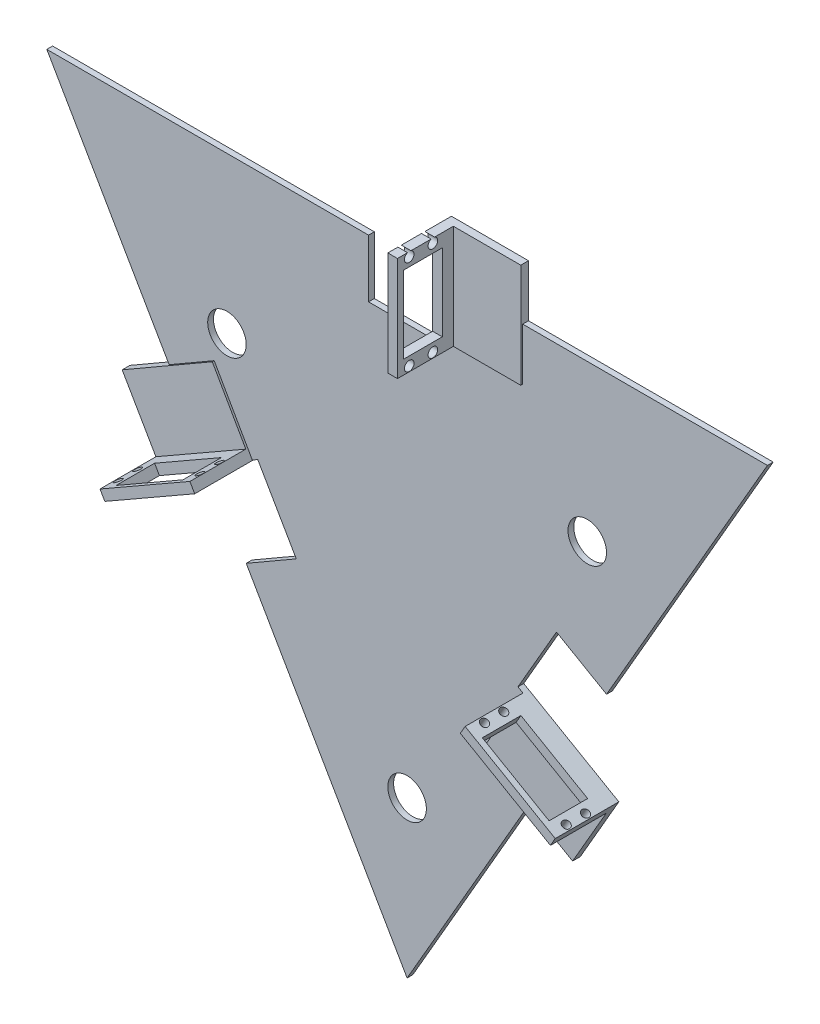
SolidWorks part; units mm, degrees
ref_plane "Front Plane" through (0, 0, 0) normal (0, 0, 1) x (1, 0, 0)
ref_plane "Top Plane" through (0, 0, 0) normal (0, 1, 0) x (1, 0, 0)
ref_plane "Right Plane" through (0, 0, 0) normal (1, 0, 0) x (0, 0, -1)
sketch "Sketch2" plane through (0, 0, 0) normal (0, 0, 1) x (1, 0, 0)
  line L0 (0, 161.9468) -> (0, -161.9468) construction
  line L1 (-187, 161.9468) -> (187, 161.9468)
  line L2 (187, 161.9468) -> (0, -161.9468)
  line L3 (-187, 161.9468) -> (0, -161.9468)
  point P4 (0, 0)
  point P8 (0, 161.9468)
  dimension "D1" = 374
  dimension "D2" = 374
  dimension "D3" = 374
extrude "Boss-Extrude1" add sketch "Sketch2" along normal blind 3
sketch "Sketch3" plane through (0, 0, 0) normal (0, 0, 1) x (1, 0, 0)
  line L1 (-187, 161.9468) -> (0, -161.9468) construction
  line L2 (-83.5, -17.3205) -> (-57.5192, -2.3205)
  line L6 (-103.5, 17.3205) -> (-77.5192, 32.3205)
  line L9 (0, -161.9468) -> (187, 161.9468) construction
  line L11 (57.5192, -2.3205) -> (83.5, -17.3205)
  line L13 (103.5, 17.3205) -> (77.5192, 32.3205)
  line L16 (187, 161.9468) -> (-187, 161.9468) construction
  line L18 (20, 131.9468) -> (20, 161.9468)
  line L20 (-20, 161.9468) -> (-20, 131.9468)
  line L22 (-103.5, 17.3205) -> (-83.5, -17.3205)
  line L23 (83.5, -17.3205) -> (103.5, 17.3205)
  line L24 (-20, 161.9468) -> (20, 161.9468)
  line L25 (-77.5192, 32.3205) -> (-57.5192, -2.3205)
  line L26 (-20, 161.9468) -> (20, 161.9468)
  line L27 (-20, 161.9468) -> (-20, 131.9468)
  line L28 (-20, 131.9468) -> (20, 131.9468)
  line L29 (20, 161.9468) -> (20, 131.9468)
  line L30 (77.5192, 32.3205) -> (57.5192, -2.3205)
  dimension "D1" = 30
  dimension "D4" = 30
  dimension "D6" = 30
extrude "Cut-Extrude2" cut sketch "Sketch3" along normal blind 10 contours L30 L11 L23 L13 | L25 L2 L22 L6
sketch "Sketch4" plane through (0, 0, 0) normal (0, 0, 1) x (1, 0, 0)
  line L1 (187, 161.9468) -> (-187, 161.9468) construction
  line L2 (0, 131.9468) -> (20, 131.9468)
  line L3 (20, 131.9468) -> (20, 161.9468)
  line L4 (20, 161.9468) -> (0, 161.9468)
  line L5 (0, 161.9468) -> (-20, 161.9468)
  line L6 (-20, 161.9468) -> (-20, 131.9468)
  line L7 (-20, 131.9468) -> (0, 131.9468)
  dimension "D1" = 20
  dimension "D2" = 20
  dimension "D3" = 30
extrude "Cut-Extrude3" cut sketch "Sketch4" along normal blind 10
sketch "Sketch5" plane through (0, 0, 0) normal (0, 0, 1) x (1, 0, 0)
  line L0 (-103.5, 17.3205) -> (-80.2543, 30.544)
  line L1 (-80.2543, 30.544) -> (-100.1173, 65.4615)
  line L2 (-100.1173, 65.4615) -> (-123.5, 51.9615)
  line L3 (-187, 161.9468) -> (-103.5, 17.3205) construction
  line L5 (-103.5, 17.3205) -> (-126.8827, 3.8205)
  line L6 (-126.8827, 3.8205) -> (-146.8827, 38.4615)
  line L7 (-146.8827, 38.4615) -> (-123.5, 51.9615)
  line L16 (20, 161.9468) -> (20, 134.9468)
  line L17 (20, 134.9468) -> (60, 134.9468)
  line L18 (60, 134.9468) -> (60, 161.9468)
  line L19 (187, 161.9468) -> (20, 161.9468) construction
  line L21 (20, 161.9468) -> (20, 188.9468)
  line L22 (20, 188.9468) -> (60, 188.9468)
  line L23 (60, 188.9468) -> (60, 161.9468)
  line L24 (83.5, -17.3205) -> (60.1173, -3.8205)
  line L25 (60.1173, -3.8205) -> (40.1173, -38.4615)
  line L26 (40.1173, -38.4615) -> (63.5, -51.9615)
  line L27 (0, -161.9468) -> (83.5, -17.3205) construction
  line L29 (83.5, -17.3205) -> (106.8827, -30.8205)
  line L30 (106.8827, -30.8205) -> (86.8827, -65.4615)
  line L31 (86.8827, -65.4615) -> (63.5, -51.9615)
  dimension "D1" = 40
  dimension "D2" = 27
  dimension "D3" = 27
  dimension "D7" = 27
  dimension "D8" = 27
  dimension "D9" = 40
  dimension "D10" = 40
  dimension "D11" = 27
  dimension "D12" = 27
extrude "Boss-Extrude2" add sketch "Sketch5" along normal blind 4
sketch "Sketch6" plane through (0, 0, 3) normal (0, 0, 1) x (1, 0, 0)
  line L0 (-126.8827, 3.8205) -> (-80.2543, 30.544)
  line L1 (-80.2543, 30.544) -> (-82.7265, 34.89)
  line L2 (-80.2543, 30.544) -> (-100.1173, 65.4615) construction
  line L3 (-82.7265, 34.89) -> (-129.3827, 8.1506)
  line L4 (-146.8827, 38.4615) -> (-126.8827, 3.8205) construction
  line L5 (-129.3827, 8.1506) -> (-126.8827, 3.8205)
  line L6 (60.1173, -3.8205) -> (106.8827, -30.8205)
  line L7 (106.8827, -30.8205) -> (104.3827, -35.1506)
  line L8 (86.8827, -65.4615) -> (106.8827, -30.8205) construction
  line L12 (20, 134.9468) -> (20, 188.9468)
  line L13 (20, 188.9468) -> (25, 188.9468)
  line L14 (60, 188.9468) -> (20, 188.9468) construction
  line L15 (25, 188.9468) -> (25, 134.9468)
  line L16 (20, 134.9468) -> (60, 134.9468) construction
  line L17 (25, 134.9468) -> (20, 134.9468)
  line L18 (104.3827, -35.1506) -> (57.6173, -8.1506)
  line L19 (60.1173, -3.8205) -> (40.1173, -38.4615) construction
  line L20 (57.6173, -8.1506) -> (60.1173, -3.8205)
  dimension "D1" = 5
  dimension "D2" = 5
  dimension "D3" = 5
  dimension "D4" = 5
extrude "Boss-Extrude3" add sketch "Sketch6" along normal blind 30
sketch "Sketch8" plane through (-33.0199, 57.6147, 0) normal (0.4972, -0.8676, 0) x (0.8676, 0.4972, 0)
  line L0 (-108.2287, 20.7043) -> (-54.2287, 20.7043) construction
  line L1 (-101.2287, 30.7043) -> (-61.2287, 30.7043)
  line L2 (-101.2287, 30.7043) -> (-101.2287, 10.7043)
  line L3 (-101.2287, 10.7043) -> (-61.2287, 10.7043)
  line L4 (-61.2287, 30.7043) -> (-61.2287, 10.7043)
  line L5 (-101.2287, 30.7043) -> (-61.2287, 10.7043) construction
  line L6 (-101.2287, 10.7043) -> (-61.2287, 30.7043) construction
  circle A0 centre (-56.7287, 15.7043) radius 2
  circle A1 centre (-56.7287, 25.7043) radius 2
  circle A2 centre (-105.7287, 25.7043) radius 2
  circle A3 centre (-105.7287, 15.7043) radius 2
  point P3 (-81.2287, 20.7043)
  point P8 (-81.2287, 20.7043)
  dimension "D1" = 5
  dimension "D2" = 5
  dimension "D3" = 4.5
  dimension "D4" = 4.5
  dimension "D5" = 4.5
  dimension "D6" = 5
  dimension "D7" = 5
  dimension "D8" = 4.5
extrude "Cut-Extrude4" cut sketch "Sketch8" against normal blind 40
sketch "Sketch9" plane through (10.875, 18.8361, 0) normal (-0.5, -0.866, 0) x (0.866, -0.5, 0)
  line L0 (54.7934, 20.1283) -> (107.1502, 20.1283) construction
  line L1 (60.9718, 30.1283) -> (100.9718, 30.1283)
  line L2 (60.9718, 30.1283) -> (60.9718, 10.1283)
  line L3 (60.9718, 10.1283) -> (100.9718, 10.1283)
  line L4 (100.9718, 30.1283) -> (100.9718, 10.1283)
  line L5 (60.9718, 30.1283) -> (100.9718, 10.1283) construction
  line L6 (60.9718, 10.1283) -> (100.9718, 30.1283) construction
  circle A0 centre (105.4718, 15.1283) radius 2
  circle A1 centre (105.4718, 25.1283) radius 2
  circle A2 centre (56.4718, 25.1283) radius 2
  circle A3 centre (56.4718, 15.1283) radius 2
  point P3 (80.9718, 20.1283)
  point P8 (80.9718, 20.1283)
  dimension "D1" = 5
  dimension "D2" = 5
  dimension "D3" = 4.5
  dimension "D4" = 4.5
  dimension "D5" = 4.5
  dimension "D6" = 5
  dimension "D7" = 5
  dimension "D8" = 4.5
extrude "Cut-Extrude5" cut sketch "Sketch9" against normal blind 40
sketch "Sketch13" plane through (25, 0, 0) normal (1, 0, 0) x (0, 0, -1)
  line L8 (-9.7559, 182.1089) -> (-29.7559, 182.1089)
  line L9 (-9.7559, 182.1089) -> (-9.7559, 142.1089)
  line L10 (-9.7559, 142.1089) -> (-29.7559, 142.1089)
  line L11 (-29.7559, 182.1089) -> (-29.7559, 142.1089)
  circle A4 centre (-26.8908, 137.6089) radius 2.5
  circle A5 centre (-14.6323, 137.6089) radius 2.5
  circle A6 centre (-26.8908, 186.6089) radius 2.5
  circle A7 centre (-14.6323, 186.6089) radius 2.5
  dimension "D11" = 5
  dimension "D12" = 5
  dimension "D15" = 5
  dimension "5" = 5
  dimension "D9" = 20
  dimension "D10" = 40
  dimension "D13" = 4.5
  dimension "D14" = 4.5
  dimension "D16" = 4.5
  dimension "D17" = 4.5
extrude "Cut-Extrude6" cut sketch "Sketch13" against normal blind 40
sketch "Sketch14" plane through (0, 0, 0) normal (0, 0, -1) x (-1, 0, 0)
  circle A0 centre (0, -80.9734) radius 10
  circle A1 centre (93.5, 80.9734) radius 10
  circle A2 centre (-93.5, 80.9734) radius 10
  dimension "D1" = 20
  dimension "D2" = 20
  dimension "D3" = 20
extrude "Cut-Extrude7" cut sketch "Sketch14" against normal blind 10
sketch "Sketch15" plane through (0, 0, 0) normal (0, 0, -1) x (-1, 0, 0)
  line L0 (0, -80.9734) -> (93.5, 80.9734) construction
  line L1 (93.5, 80.9734) -> (-93.5, 80.9734) construction
  line L2 (-93.5, 80.9734) -> (0, -80.9734) construction
  dimension "D1" = 187
